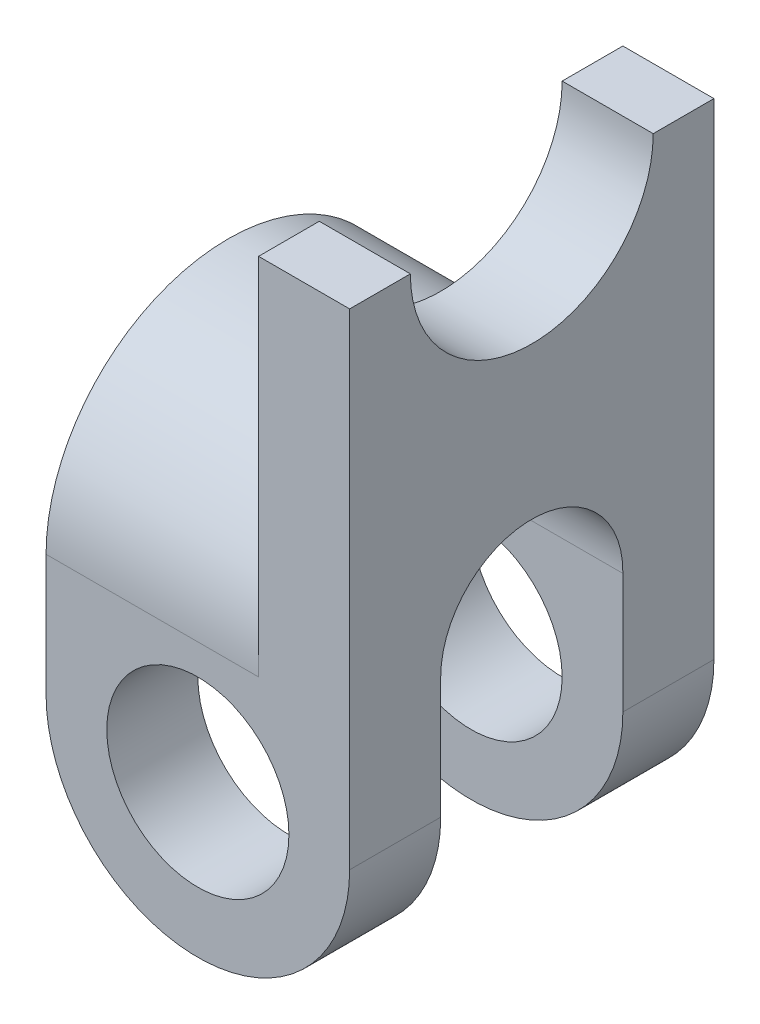
SolidWorks part; units mm, degrees
ref_plane "Front Plane" through (0, 0, 0) normal (0, 0, 1) x (1, 0, 0)
ref_plane "Top Plane" through (0, 0, 0) normal (0, 1, 0) x (1, 0, 0)
ref_plane "Right Plane" through (0, 0, 0) normal (1, 0, 0) x (0, 0, -1)
sketch "Sketch1" plane through (0, 0, 0) normal (0, 0, 1) x (1, 0, 0)
  line L0 (25, 0) -> (25, 80)
  line L1 (25, 80) -> (10, 80)
  line L2 (10, 80) -> (10, 22.9129)
  line L3 (-25, 0) -> (-25, 20)
  line L4 (-25, 20) -> (10, 20)
  line L5 (10, 22.9129) -> (10, 20)
  circle A0 centre (0, 0) radius 15
  arc A1 (-25, 0) -> (25, 0) centre (0, 0) ccw
  dimension "D1" = 30
  dimension "D2" = 50
  dimension "D3" = 80
  dimension "D4" = 15
  dimension "D5" = 20
extrude "Boss-Extrude1" add sketch "Sketch1" along normal mid plane 60
sketch "Sketch2" plane through (10, 0, 0) normal (-1, 0, 0) x (0, 0, 1)
  line L0 (30, 80) -> (-30, 80) construction
  circle A0 centre (0, 80) radius 20
  dimension "D1" = 40
extrude "Cut-Extrude1" cut sketch "Sketch2" against normal through all
sketch "Sketch4" plane through (-25, 0, 0) normal (-1, 0, 0) x (0, 0, 1)
  line L0 (30, 20) -> (-30, 20) construction
  line L1 (-15, 20) -> (-30, 20)
  line L2 (15, 20) -> (30, 20)
  arc A0 (15, 20) -> (-15, 20) centre (0, 20) ccw
  arc A1 (30, 20) -> (-30, 20) centre (0, 20) ccw
  dimension "D1" = 30
extrude "Boss-Extrude2" add sketch "Sketch4" against normal up to surface (35 mm away) up to face at (10, 56.6667, 0)
sketch "Sketch5" plane through (-25, 0, 0) normal (-1, 0, 0) x (0, 0, 1)
  line L0 (15, 20) -> (-15, 20) construction
  line L1 (-15, 19.7744) -> (-15, -47.367)
  line L2 (15.0017, 20) -> (15.0017, -44.5845)
  line L3 (-15, -47.367) -> (15.0017, -47.367)
  line L4 (15.0017, -47.367) -> (15.0017, -44.5845)
  arc A0 (15.0017, 20) -> (-15, 19.7744) centre (0, 20) ccw
extrude "Cut-Extrude3" cut sketch "Sketch5" against normal through all
